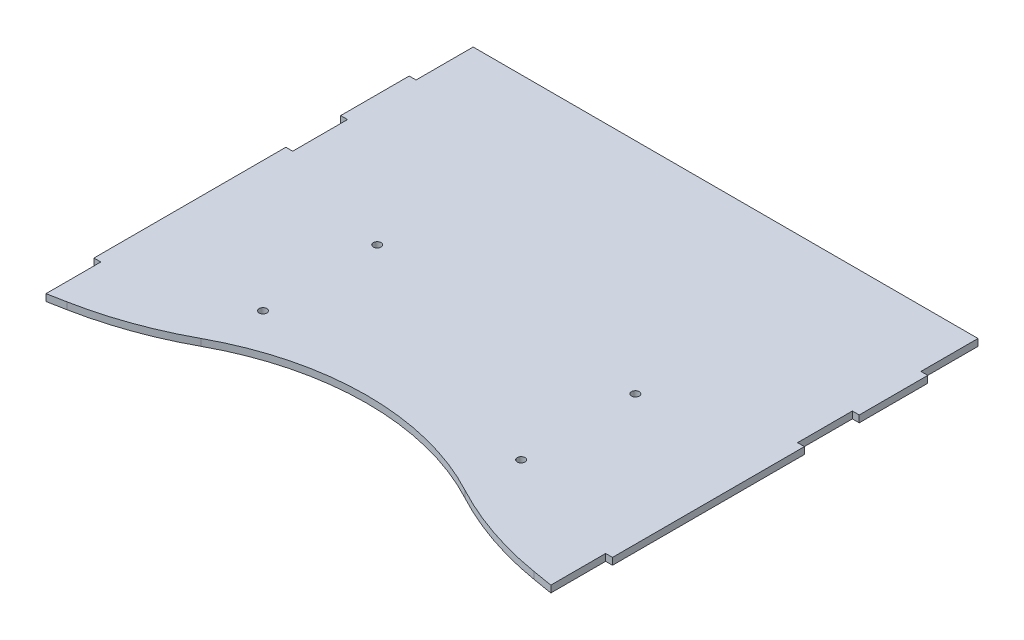
SolidWorks part; units mm, degrees
ref_plane "Alzado" through (0, 0, 0) normal (0, 0, 1) x (1, 0, 0)
ref_plane "Planta" through (0, 0, 0) normal (0, 1, 0) x (1, 0, 0)
ref_plane "Vista lateral" through (0, 0, 0) normal (1, 0, 0) x (0, 0, -1)
sketch "Croquis1" plane through (0, 0, 0) normal (0, 1, 0) x (1, 0, 0)
  line L0 (11.1224, -66.347) -> (11.1224, 64.0059) construction
  line L11 (-99.3776, 10.0059) -> (-102.3776, 10.0059)
  line L12 (-102.3776, 10.0059) -> (-102.3776, -73.9941)
  line L13 (-102.3776, -73.9941) -> (-99.3776, -73.9941)
  line L31 (-99.3776, 10.0059) -> (-99.3776, 34.0059)
  line L33 (-102.3776, -31.9941) -> (-30.175, -31.9943) construction
  line L34 (-45.3779, -6.9943) -> (-45.378, -56.9943) construction
  line L35 (-99.3776, 34.0059) -> (-102.3776, 34.0059)
  line L36 (-102.3776, 34.0059) -> (-102.3776, 64.0059)
  line L38 (-99.3776, -73.9941) -> (-99.3776, -97.9941)
  line L42 (124.6224, 34.0059) -> (124.6224, 64.0059)
  line L43 (67.6228, -6.9943) -> (67.6229, -56.9943) construction
  line L44 (124.6224, -31.9941) -> (52.4199, -31.9943) construction
  line L46 (121.6224, -73.9941) -> (121.6224, -97.9941)
  line L47 (121.6224, 34.0059) -> (124.6224, 34.0059)
  line L48 (121.6224, 10.0059) -> (121.6224, 34.0059)
  line L49 (124.6224, -73.9941) -> (121.6224, -73.9941)
  line L50 (124.6224, 10.0059) -> (124.6224, -73.9941)
  line L51 (121.6224, 10.0059) -> (124.6224, 10.0059)
  line L52 (-99.3776, -97.9941) -> (-91.7406, -96.5297)
  line L54 (121.6224, -97.9941) -> (112.8906, -96.5297)
  line L55 (-99.3776, 89.0058) -> (121.6224, 89.0051)
  line L66 (-102.3776, 64.0059) -> (-99.3776, 64.0059)
  line L68 (124.6224, 64.0059) -> (121.6224, 64.0059)
  line L69 (121.6224, 64.0059) -> (121.6224, 89.0051)
  line L71 (-99.3776, 64.0059) -> (-99.3776, 89.0058)
  circle A17 centre (-45.378, -56.9943) radius 1.7
  circle A18 centre (-45.3779, -6.9943) radius 1.7
  circle A19 centre (67.6228, -6.9943) radius 1.7
  circle A20 centre (67.6229, -56.9943) radius 1.7
  arc A21 (66.7384, -80.7488) -> (-48.3937, -81.0248) centre (9.4279, -187.479) ccw
  arc A22 (112.8906, -96.5297) -> (66.7384, -80.7488) centre (137.7, 51.4043) cw
  arc A23 (-91.7406, -96.5297) -> (-48.3937, -81.0248) centre (-119.9883, 50.7865) ccw
  point P8 (11.1224, 64.0059)
  point P30 (-43.1567, -54)
  point P33 (65.4016, -54)
  dimension "D1" = 150
  dimension "D2" = 227
  dimension "D3" = 227
  dimension "D5" = 56.9997
extrude "Saliente-Extruir1" add sketch "Croquis1" along normal blind 3
